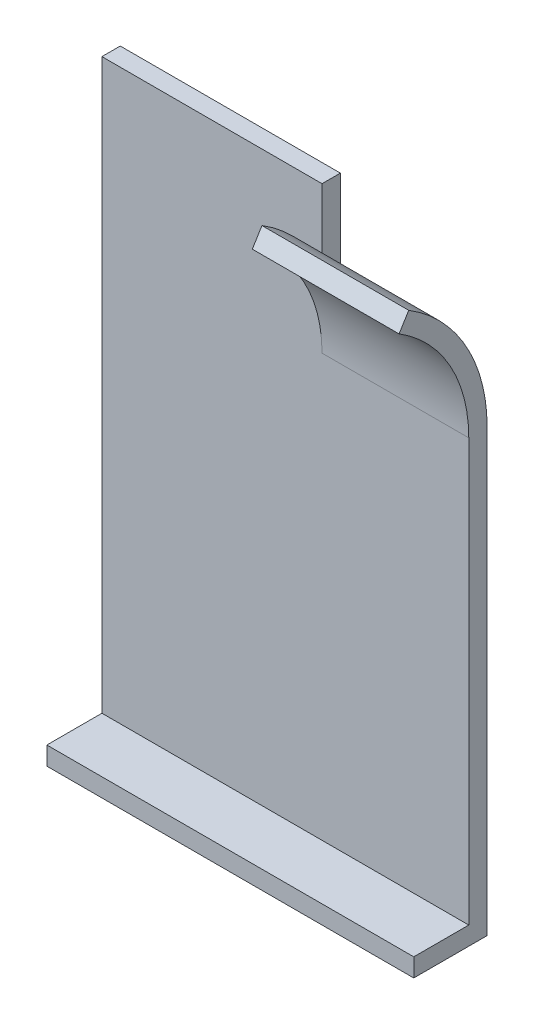
SolidWorks part; units mm, degrees
ref_plane "Front Plane" through (0, 0, 0) normal (0, 0, 1) x (1, 0, 0)
ref_plane "Top Plane" through (0, 0, 0) normal (0, 1, 0) x (1, 0, 0)
ref_plane "Right Plane" through (0, 0, 0) normal (1, 0, 0) x (0, 0, -1)
sketch "Sketch1" plane through (0, 0, 0) normal (0, 0, 1) x (1, 0, 0)
  line L0 (0, 101.6) -> (38.1, 101.6)
  line L1 (0, 0) -> (63.5, 0) construction
  line L2 (0, 0) -> (0, 101.6)
  line L3 (0, 101.6) -> (63.5, 101.6) construction
  line L4 (63.5, 0) -> (63.5, 101.6) construction
  line L5 (38.1, 101.6) -> (38.1, 76.2)
  line L6 (38.1, 76.2) -> (63.5, 76.2)
  line L7 (63.5, 76.2) -> (63.5, 0)
  line L8 (63.5, 0) -> (0, 0)
  dimension "D1" = 63.5
  dimension "D2" = 101.6
  dimension "D3" = 38.1
  dimension "D4" = 25.4
extrude "Boss-Extrude1" add sketch "Sketch1" along normal blind 3.175
sketch "Sketch2" plane through (63.5, 0, 0) normal (1, 0, 0) x (0, 0, -1)
  line L0 (-3.175, 76.2) -> (0, 76.2)
  line L1 (0, 0) -> (0, 76.2) construction
  line L2 (-15.24, 97.818) -> (-13.5731, 100.5202)
  line L3 (-28.575, 76.2) -> (-15.24, 97.818) construction
  line L4 (-3.175, 0) -> (-3.175, 76.2) construction
  arc A0 (-3.175, 76.2) -> (-15.24, 97.818) centre (-28.575, 76.2) ccw
  arc A1 (0, 76.2) -> (-13.5731, 100.5202) centre (-28.575, 76.2) ccw
  dimension "D2" = 25.4
  dimension "D1" = 15.24
extrude "Boss-Extrude2" add sketch "Sketch2" against normal up to surface (25.4 mm away) up to face at (38.1, 88.9, 1.5875)
sketch "Sketch4" plane through (63.5, 0, 0) normal (1, 0, 0) x (0, 0, -1)
  line L0 (0, 0) -> (-12.7, 0)
  line L1 (-12.7, 0) -> (-12.7, 3.175)
  line L2 (-12.7, 3.175) -> (0, 3.175)
  line L3 (0, 0) -> (0, 76.2) construction
  line L4 (0, 3.175) -> (0, 0)
  dimension "D1" = 3.175
  dimension "D2" = 12.7
extrude "Boss-Extrude3" add sketch "Sketch4" against normal up to surface (63.5 mm away) up to face at (0, 50.8, 1.5875)
